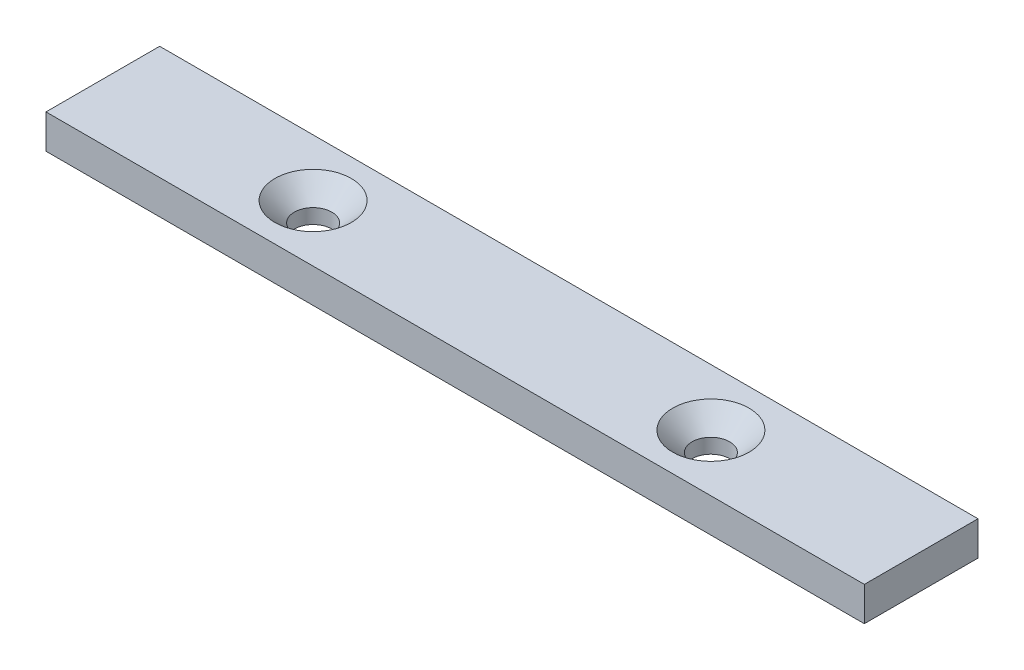
SolidWorks part; units mm, degrees
material "AISI 1020"
ref_plane "Front" through (0, 0, 0) normal (0, 0, 1) x (1, 0, 0)
ref_plane "Top" through (0, 0, 0) normal (0, 1, 0) x (1, 0, 0)
ref_plane "Right" through (0, 0, 0) normal (1, 0, 0) x (0, 0, -1)
sketch "Sketch1" plane through (0, 0, 0) normal (0, 1, 0) x (1, 0, 0)
  line L0 (-72, -10) -> (-72, 10)
  line L1 (-72, 10) -> (72, 10)
  line L2 (72, -10) -> (-72, 10) construction
  line L3 (-72, -10) -> (72, -10)
  line L4 (72, 10) -> (72, -10)
  dimension "D1" = 144
  dimension "D2" = 20
extrude "Extrude1" add sketch "Sketch1" along normal blind 6
hole_wizard "Escareado para SFHCS M61" positions "Esboço2" profile "Esboço1" countersink size "M6" standard "Métrico Ansi" end condition through all
sketch "Esboço2" plane through (0, 6, 0) normal (0, 1, 0) x (-1, 0, 0)
  point P0 (35, 0)
  point P1 (-35, 0)
  point P11 (34.7891, 0)
  dimension "D1" = 70
  dimension "D2" = 35
sketch "Esboço1" plane through (-35, 6, 0) normal (1, 0, 0) x (0, 0, 1)
  line L0 (0, 0) -> (0, 6)
  line L1 (0, 6) -> (3.3, 6)
  line L2 (3.3, 6) -> (3.3, 3.42)
  line L3 (3.3, 3.42) -> (6.72, 0)
  line L5 (6.72, 0) -> (0, 0)
  line L6 (-3.3, 3.42) -> (-6.72, 0) construction
  line L11 (0, -6.35) -> (0, 107.95) construction
  dimension "Thru Hole Dia." = 6.6
  dimension "Thru Hole Depth" = 6
  dimension "Near C'Sink Dia." = 13.44
  dimension "Near C'Sink Angle" = 90
